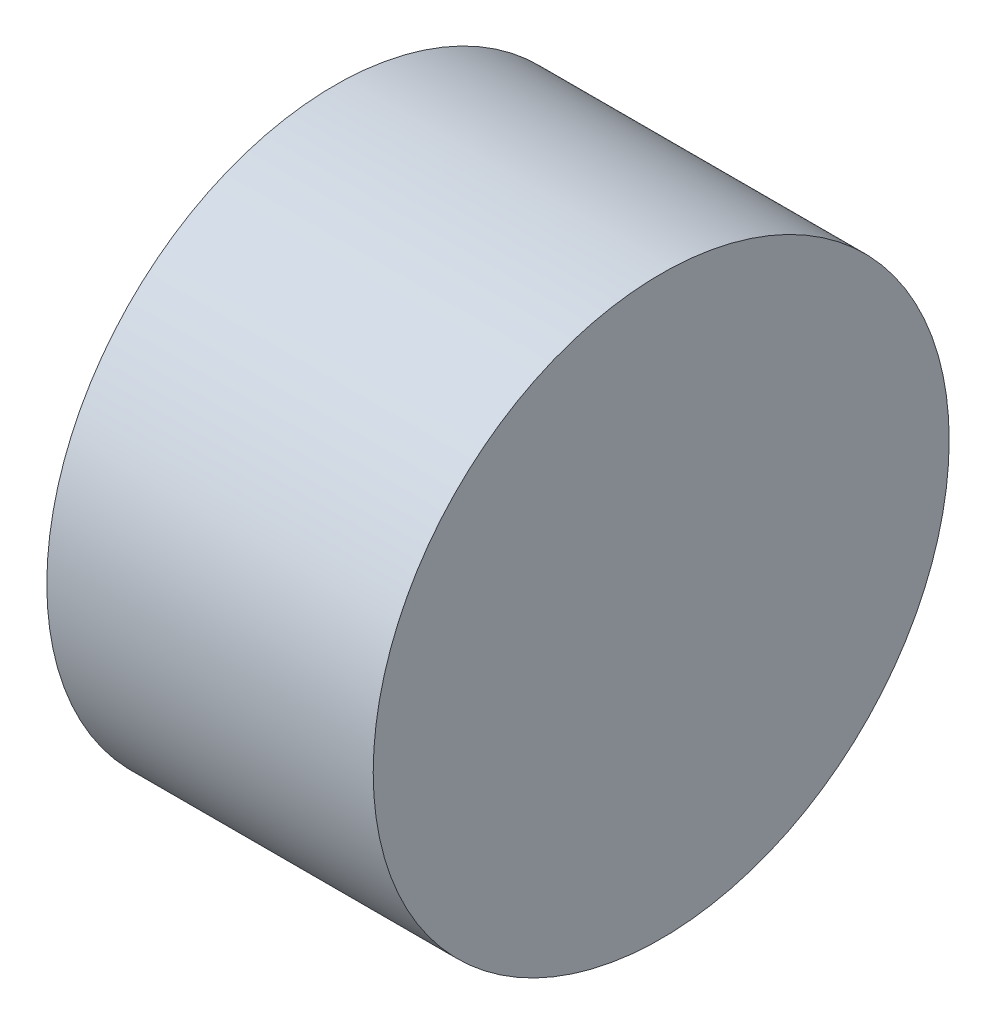
SolidWorks part; units mm, degrees
ref_plane "Front Plane" through (0, 0, 0) normal (0, 0, 1) x (1, 0, 0)
ref_plane "Top Plane" through (0, 0, 0) normal (0, 1, 0) x (1, 0, 0)
ref_plane "Right Plane" through (0, 0, 0) normal (1, 0, 0) x (0, 0, -1)
sketch "Sketch1" plane through (0, 0, 0) normal (1, 0, 0) x (0, 0, -1)
  circle A0 centre (0, 0) radius 3
  dimension "D1" = 6
extrude "Boss-Extrude1" add sketch "Sketch1" along normal blind 3.4
ref_plane "Plane1" through (0, 0, 0) normal (0, 1, 0) x (1, 0, 0)
